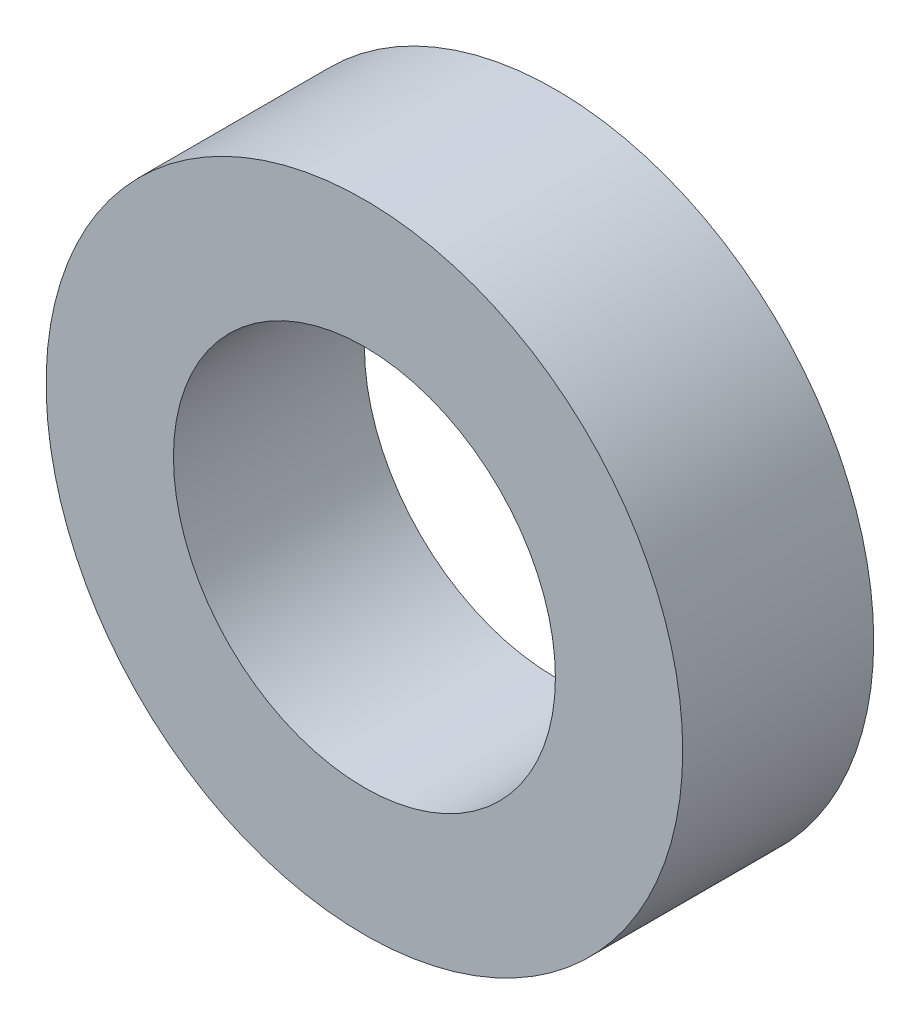
SolidWorks part; units mm, degrees
ref_plane "前视基准面" through (0, 0, 0) normal (0, 0, 1) x (1, 0, 0)
ref_plane "上视基准面" through (0, 0, 0) normal (0, 1, 0) x (1, 0, 0)
ref_plane "右视基准面" through (0, 0, 0) normal (1, 0, 0) x (0, 0, -1)
sketch "草图1" plane through (0, 0, 0) normal (0, 0, 1) x (1, 0, 0)
  circle A0 centre (0, 0) radius 3
  circle A1 centre (0, 0) radius 5
extrude "凸台-拉伸1" add sketch "草图1" along normal blind 3
